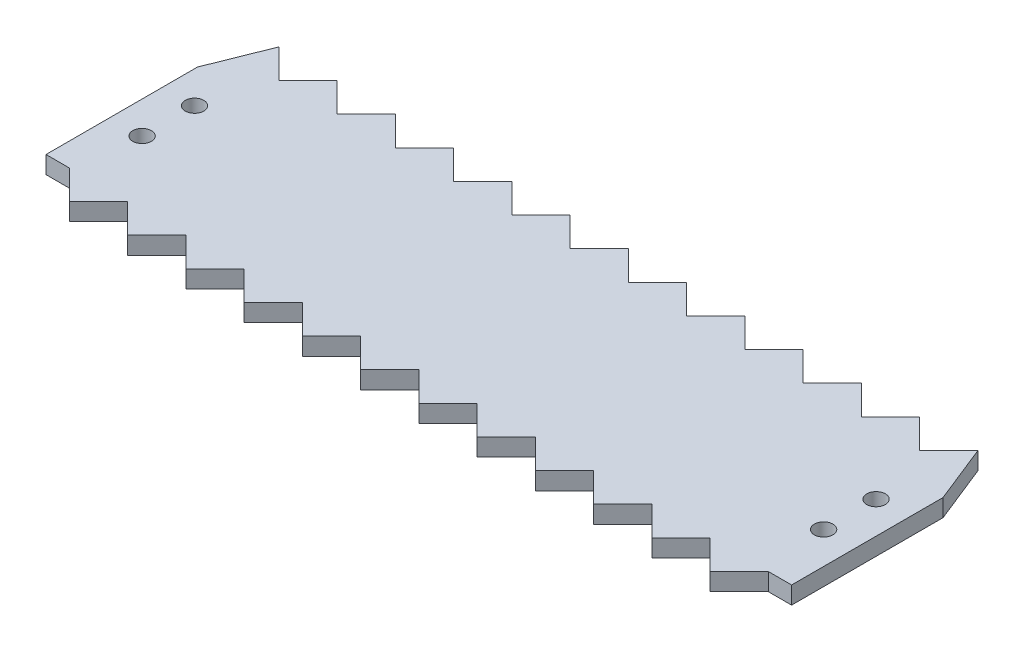
SolidWorks part; units mm, degrees
ref_plane "Front Plane" through (0, 0, 0) normal (0, 0, 1) x (1, 0, 0)
ref_plane "Top Plane" through (0, 0, 0) normal (0, 1, 0) x (1, 0, 0)
ref_plane "Right Plane" through (0, 0, 0) normal (1, 0, 0) x (0, 0, -1)
sketch "Sketch1" plane through (0, 0, 0) normal (0, 1, 0) x (1, 0, 0)
  line L1 (-64, -20.5) -> (64, -20.5)
  line L2 (-64, -20.5) -> (-64, 20.5)
  line L3 (-64, 20.5) -> (64, 20.5)
  line L4 (64, -20.5) -> (64, 20.5)
  line L5 (-64, -20.5) -> (64, 20.5) construction
  line L6 (-64, 20.5) -> (64, -20.5) construction
  point P0 (0, 0)
  dimension "D1" = 128
  dimension "D2" = 41
extrude "Boss-Extrude1" add sketch "Sketch1" along normal blind 3
sketch "Sketch2" plane through (0, 3, 0) normal (0, 1, 0) x (1, 0, 0)
  line L0 (-60, 20.5) -> (-55, 15.5)
  line L1 (-55, 15.5) -> (-50, 20.5)
  line L3 (64, 20.5) -> (-64, 20.5) construction
  line L4 (-50, 20.5) -> (-60, 20.5)
  line L5 (-64, 20.5) -> (-64, -20.5) construction
  dimension "D1" = 10
  dimension "D2" = 5
  dimension "D3" = 4
extrude "Cut-Extrude2" cut sketch "Sketch2" against normal through all both and the other way through all
pattern_linear "LPattern3" count 12 spacing 10 along (1, 0, 0) of "Cut-Extrude2"
sketch "Sketch5" plane through (0, 3, 0) normal (0, 1, 0) x (1, 0, 0)
  line L0 (-60, -15.5) -> (-55, -20.5)
  line L2 (-64, -20.5) -> (64, -20.5) construction
  line L3 (-55, -20.5) -> (-50, -15.5)
  line L4 (-50, -15.5) -> (-50, -20.5)
  line L5 (-50, -20.5) -> (-60, -20.5)
  line L6 (-60, -20.5) -> (-60, -15.5)
  line M27 (-64, -20.5) -> (64, -20.5)
  dimension "D1" = 10
  dimension "D2" = 5
  dimension "D3" = 4
extrude "Cut-Extrude3" cut sketch "Sketch5" against normal through all both and the other way through all contours L6 L0 M27 | L4 L3 M27
pattern_linear "LPattern5" count 12 spacing 10 along (1, 0, 0) of "Cut-Extrude3"
sketch "Sketch6" plane through (0, 3, 0) normal (0, 1, 0) x (1, 0, 0)
  circle A0 centre (-58.5, 4.5) radius 1.6
  dimension "D1" = 3.2
  dimension "D2" = 58.5
  dimension "D3" = 4.5
extrude "Cut-Extrude4" cut sketch "Sketch6" against normal through all both and the other way through all
mirror "Mirror2" about plane through (0, 0, 0) normal (1, 0, 0) of "Cut-Extrude4"
mirror "Mirror3" about plane through (0, 0, 0) normal (0, 0, 1) of "Mirror2", "Cut-Extrude4"
sketch "Sketch7" plane through (0, 3, 0) normal (0, 1, 0) x (1, 0, 0)
  line L0 (-60, 20.5) -> (-64, 10.5)
  line L1 (-64, 20.5) -> (-64, -20.5) construction
  line L2 (-64, 10.5) -> (-64, 20.5)
  line L3 (-64, 20.5) -> (-60, 20.5)
  dimension "D1" = 10
extrude "Cut-Extrude5" cut sketch "Sketch7" against normal through all both and the other way through all
mirror "Mirror4" about plane through (0, 0, 0) normal (1, 0, 0) of "Cut-Extrude5"
sketch "Sketch8" plane through (0, 3, 0) normal (0, 1, 0) x (1, 0, 0)
  line L1 (-60, -15.5) -> (-64, -15.5)
  line L2 (-60, -15.5) -> (-60, -20.5)
  line L3 (-60, -20.5) -> (-64, -20.5)
  line L4 (-64, -15.5) -> (-64, -20.5)
extrude "Cut-Extrude6" cut sketch "Sketch8" against normal through all both and the other way through all
mirror "Mirror5" about plane through (0, 0, 0) normal (1, 0, 0) of "Cut-Extrude6"
